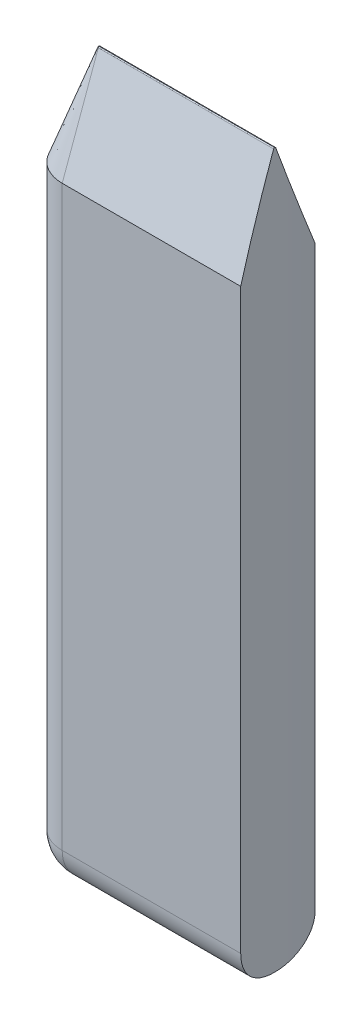
SolidWorks part; units mm, degrees
ref_plane "Front Plane" through (0, 0, 0) normal (0, 0, 1) x (1, 0, 0)
ref_plane "Top Plane" through (0, 0, 0) normal (0, 1, 0) x (1, 0, 0)
ref_plane "Right Plane" through (0, 0, 0) normal (1, 0, 0) x (0, 0, -1)
sketch "Sketch1" plane through (0, 0, 0) normal (0, 1, 0) x (1, 0, 0)
  line L0 (0, 30) -> (0, -30) construction
  line L1 (0, 0) -> (-29.5442, 5.2094)
  line L2 (-30, 0) -> (30, 0) construction
  line L3 (0, 0) -> (-29.5442, -5.2094)
  line L4 (-29.5442, 5.2094) -> (-54.5442, 5.2094)
  line L6 (-54.5442, -5.2094) -> (-29.5442, -5.2094)
  circle A0 centre (0, 0) radius 30
  arc A1 (-54.5442, 5.2094) -> (-54.5442, -5.2094) centre (-54.5442, 0) ccw
  dimension "D1" = 20
  dimension "D2" = 10
  dimension "D3" = 25
extrude "Boss-Extrude1" add sketch "Sketch1" along normal blind 100 contours L4 A1 L6 A0
chamfer "Chamfer1" distance 14 angle 20 3 edges at (-42.0442, 100, 5.2094) (-59.7537, 100, 0) (-42.0442, 100, -5.2094)
fillet "Fillet1" radius 0.15 3 edges at (-42.272, 100, -0.1139) (-54.6581, 100, 0) (-42.272, 100, 0.1139)
fillet "Fillet2" radius 5.1 3 edges at (-42.0442, 0, 5.2094) (-59.7537, 0, 0) (-42.0442, 0, -5.2094)
